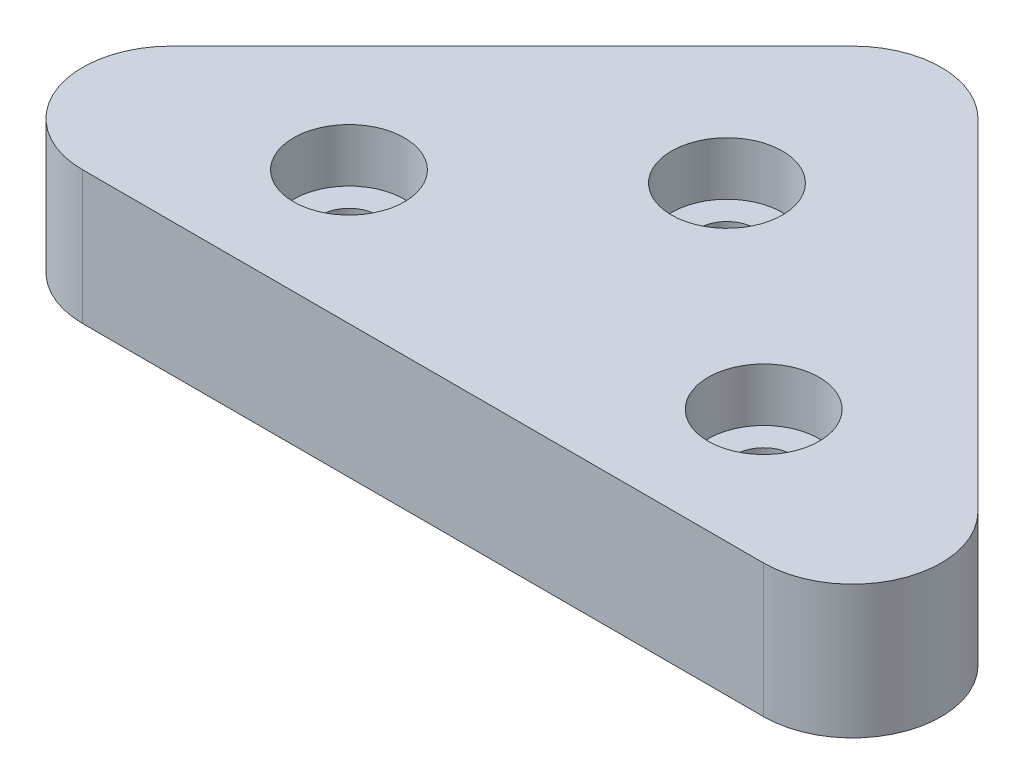
SolidWorks part; units mm, degrees
ref_plane "Front Plane" through (0, 0, 0) normal (0, 0, 1) x (1, 0, 0)
ref_plane "Top Plane" through (0, 0, 0) normal (0, 1, 0) x (1, 0, 0)
ref_plane "Right Plane" through (0, 0, 0) normal (1, 0, 0) x (0, 0, -1)
sketch "Sketch2" plane through (0, 0, 0) normal (0, 1, 0) x (1, 0, 0)
  line L0 (0, 0) -> (15.875, 15.875)
  line L1 (15.875, 15.875) -> (31.75, 0)
  line L2 (31.75, 0) -> (0, 0)
  line L3 (0, 0) -> (0.7207, -0.9009)
  dimension "D1" = 45
  dimension "D2" = 45
  dimension "D3" = 31.75
extrude "Boss-Extrude1" add sketch "Sketch2" along normal blind 3.81 contours L2 L1 L0
fillet "Fillet1" radius 2.54 3 edges at (15.875, 1.905, -15.875) (0, 1.905, 0) (31.75, 1.905, 0)
sketch "Sketch3" plane through (0, 3.81, 0) normal (0, 1, 0) x (1, 0, 0)
  line L0 (25.6179, 0) -> (6.1321, 0) construction
  point P0 (9.9421, 3.81)
  point P1 (21.8079, 3.81)
  point P2 (15.6774, 8.89)
  dimension "D2" = 3.81
  dimension "D5" = 3.81
  dimension "D1" = 3.81
  dimension "D4" = 8.89
hole_wizard "CBORE for #0 Socket Head Cap Screw1" positions "Sketch7" profile "Sketch6" counterbore size "#0" standard "ANSI Inch"
sketch "Sketch7" plane through (0, 3.81, 0) normal (0, 1, 0) x (1, 0, 0)
  point P0 (9.9421, 3.81)
  point P3 (15.6774, 8.89)
  point P6 (21.8079, 3.81)
sketch "Sketch6" plane through (9.9421, 3.81, -3.81) normal (1, 0, 0) x (0, 0, 1)
  line L0 (0, 0) -> (0, 3.7866)
  line L1 (0, 3.7866) -> (0.8064, 3.302)
  line L2 (0.8064, 3.302) -> (0.8064, 1.524)
  line L3 (0.8064, 1.524) -> (1.5875, 1.524)
  line L4 (1.5875, 1.524) -> (1.5875, 0)
  line L5 (1.5875, 0) -> (0, 0)
  line L10 (0, 3.7866) -> (-0.8065, 3.302) construction
  line L11 (0, -6.35) -> (0, 107.95) construction
  dimension "Hole Dia." = 1.6129
  dimension "Hole Depth" = 3.302
  dimension "C'Bore Dia." = 3.175
  dimension "C'Bore Depth" = 1.524
  dimension "Drill Angle" = 118
